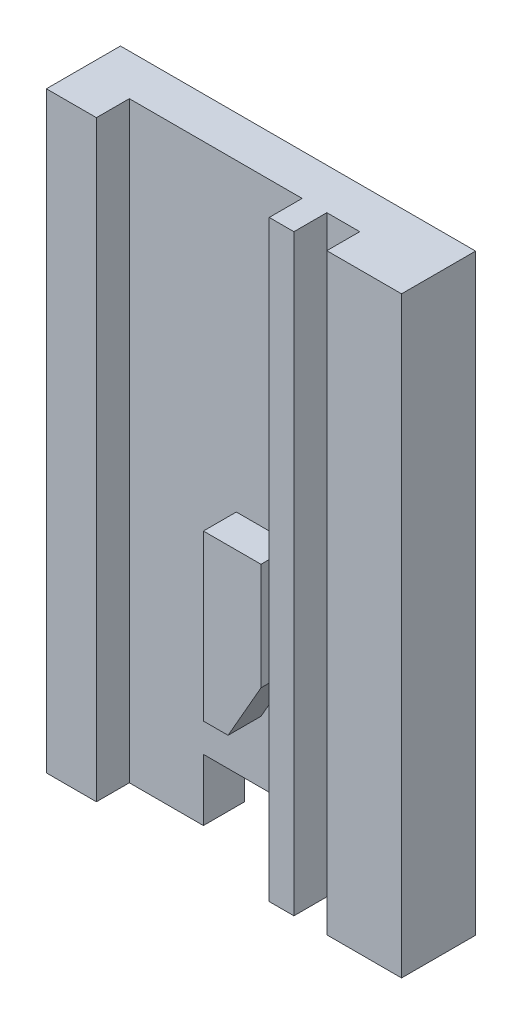
SolidWorks part; units mm, degrees
ref_plane "Front Plane" through (0, 0, 0) normal (0, 0, 1) x (1, 0, 0)
ref_plane "Top Plane" through (0, 0, 0) normal (0, 1, 0) x (1, 0, 0)
ref_plane "Right Plane" through (0, 0, 0) normal (1, 0, 0) x (0, 0, -1)
ref_plane "Plane1" through (0, 0, 0) normal (0, 0, -1) x (-1, 0, 0)
sketch "Sketch1" plane through (0, 0, 0) normal (0, 0, -1) x (-1, 0, 0)
  line L0 (-21.58, 36) -> (-21.58, -36)
  line L1 (-21.58, -36) -> (21.58, -36)
  line L2 (21.58, -36) -> (21.58, 36)
  line L3 (21.58, 36) -> (-21.58, 36)
extrude "Boss-Extrude1" add sketch "Sketch1" against normal blind 9
sketch "Sketch2" plane through (0, 36, 0) normal (0, 1, 0) x (-1, 0, 0)
  line L0 (15.5, 5) -> (15.5, 9)
  line L1 (15.5, 9) -> (-21.58, 9)
  line L2 (-21.58, 9) -> (-21.58, 5)
  line L3 (-21.58, 5) -> (15.5, 5)
extrude "Cut-Extrude1" cut sketch "Sketch2" against normal through all
sketch "Sketch3" plane through (0, 0, 5) normal (0, 0, 1) x (1, 0, 0)
  line L0 (21.58, -36) -> (21.58, -28.5)
  line L1 (21.58, -28.5) -> (-6.5, -28.5)
  line L2 (-6.5, -28.5) -> (-6.5, -36)
  line L3 (-6.5, -36) -> (21.58, -36)
extrude "Cut-Extrude2" cut sketch "Sketch3" against normal through all
sketch "Sketch4" plane through (0, 0, 5) normal (0, 0, 1) x (1, 0, 0)
  line L0 (5.5, -28.5) -> (5.5, 36)
  line L1 (5.5, 36) -> (21.58, 36)
  line L2 (21.58, 36) -> (21.58, -28.5)
  line L3 (21.58, -28.5) -> (5.5, -28.5)
extrude "Boss-Extrude2" add sketch "Sketch4" along normal blind 4
sketch "Sketch5" plane through (0, -28.5, 0) normal (0, -1, 0) x (1, 0, 0)
  line L0 (21.58, 9) -> (21.58, 0)
  line L1 (21.58, 0) -> (5.5, 0)
  line L2 (5.5, 0) -> (5.5, 9)
  line L3 (5.5, 9) -> (21.58, 9)
extrude "Boss-Extrude3" add sketch "Sketch5" along normal blind 7.5
sketch "Sketch6" plane through (0, 36, 0) normal (0, 1, 0) x (-1, 0, 0)
  line L0 (-8.5, 9) -> (-12.5, 9)
  line L1 (-12.5, 9) -> (-12.5, 5)
  line L2 (-12.5, 5) -> (-8.5, 5)
  line L3 (-8.5, 5) -> (-8.5, 9)
extrude "Cut-Extrude3" cut sketch "Sketch6" against normal through all
sketch "Sketch7" plane through (0, 0, 5) normal (0, 0, 1) x (1, 0, 0)
  line L0 (-2.5, -1) -> (4.5, -1)
  line L1 (4.5, -1) -> (4.5, -14)
  line L2 (4.5, -14) -> (0.5, -21)
  line L3 (0.5, -21) -> (-2.5, -21)
  line L4 (-2.5, -21) -> (-2.5, -1)
extrude "Boss-Extrude4" add sketch "Sketch7" along normal blind 4
scale "Scale1" scale about centroid uniform scaling yes scale factor 0.25
